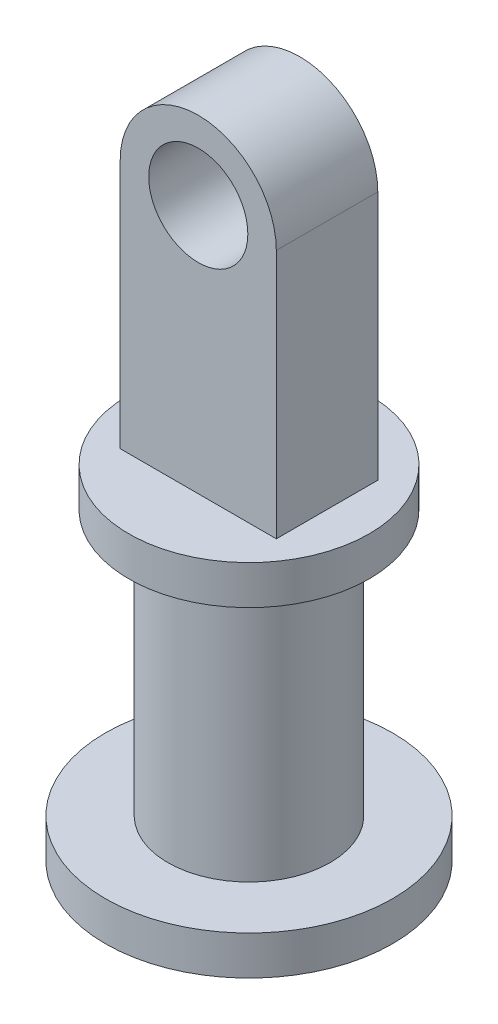
SolidWorks part; units mm, degrees
material "ABS"
ref_plane "Front Plane" through (0, 0, 0) normal (0, 0, 1) x (1, 0, 0)
ref_plane "Top Plane" through (0, 0, 0) normal (0, 1, 0) x (1, 0, 0)
ref_plane "Right Plane" through (0, 0, 0) normal (1, 0, 0) x (0, 0, -1)
sketch "Sketch1" plane through (0, 0, 0) normal (0, 0, 1) x (1, 0, 0)
  line L0 (2.5, 0) -> (2.5, -8)
  line L1 (2.5, -8) -> (-2.5, -8)
  line L2 (-2.5, -8) -> (-2.5, 0)
  arc A0 (2.5, 0) -> (-2.5, 0) centre (0, 0) ccw
  circle A1 centre (0, 0) radius 1.5875
extrude "Boss-Extrude1" add sketch "Sketch1" along normal blind 3.25
sketch "Sketch3" plane through (0, 0, 3.25) normal (0, 0, 1) x (1, 0, 0)
  line L0 (-2.5, -8) -> (-2.5, -18)
  line L1 (-2.5, -18) -> (-6.25, -18)
  line L2 (-6.25, -18) -> (-6.25, -19.5)
  line L3 (0, 0) -> (0, -8) construction
  line L4 (-2.5, -8) -> (2.5, -8) construction
  line L5 (-6.25, -19.5) -> (0.0103, -19.5)
  line L6 (2.5, -8) -> (2.5, -18)
  line L7 (6.25, -19.5) -> (-0.0103, -19.5)
  line L8 (6.25, -18) -> (6.25, -19.5)
  line L9 (2.5, -18) -> (6.25, -18)
ref_plane "Plane1" through (0, 0, 1.625) normal (0, 0, 1) x (1, 0, 0)
sketch "Sketch4" plane through (0, 0, 1.625) normal (0, 0, 1) x (1, 0, 0)
  line L0 (-2.6, -8) -> (2.6, -8)
  line L1 (-2.6, -9.25) -> (-2.6, -18)
  line L2 (-2.6, -18) -> (-4.6, -18)
  line L3 (-1.35, -19.25) -> (-4.6, -19.25)
  line L4 (4.6, -18.9948) -> (4.6, -17.7448)
  line L5 (2.6, -9.25) -> (2.6, -17.7448)
  line L6 (2.6, -17.7448) -> (4.6, -17.7448)
  line L7 (-4.6, -18) -> (-4.6, -19.25)
  line L8 (0, -19.5) -> (0, 2.5) construction
  line L9 (-1.35, -19.25) -> (-1.35, -9.25)
  line L10 (-1.35, -9.25) -> (1.35, -9.25)
  line L11 (1.35, -9.25) -> (1.35, -18.9948)
  line L12 (1.35, -18.9948) -> (4.6, -18.9948)
  line L13 (-2.5, -8) -> (2.5, -8) construction
  line L14 (2.6, -9.25) -> (3.85, -9.25)
  line L15 (3.85, -9.25) -> (3.85, -8)
  line L16 (3.85, -8) -> (2.6, -8)
  line L17 (-2.6, -8) -> (-3.85, -8)
  line L18 (-3.85, -8) -> (-3.85, -9.25)
  line L19 (-3.85, -9.25) -> (-2.6, -9.25)
  arc A0 (2.5, 0) -> (-2.5, 0) centre (0, 0) ccw construction
  point P15 (0, -8)
  dimension "D1" = 1.25
  dimension "D2" = 1.25
  dimension "D3" = 1.25
  dimension "D4" = 2.6
  dimension "D5" = 2
  dimension "D6" = 1.25
  dimension "D7" = 1.25
  dimension "D8" = 1.25
  dimension "D9" = 1.25
  dimension "D10" = 1.25
  dimension "D11" = 1.25
revolve "Revolve1" add sketch "Sketch4" angle 360 about L8
sketch "Sketch5" plane through (0, 0, 1.625) normal (0, 0, 1) x (1, 0, 0)
  line L0 (-6.35, -49.5) -> (-6.35, -16)
  line L1 (4.6, -17.7448) -> (-4.6, -17.7448) construction
  line L3 (-6.35, -16) -> (-3.1, -16)
  line L4 (-6.35, -49.5) -> (-7.85, -49.5)
  line L5 (-7.85, -49.5) -> (-7.85, -51)
  line L6 (0, 0) -> (0, -25.592) construction
  line L7 (-7.85, -51) -> (-5.1, -51)
  line L8 (-3.1, -16) -> (-3.1, -17.2448)
  line L9 (-3.1, -17.2448) -> (-5.1, -17.2448)
  line L10 (-5.1, -17.2448) -> (-5.1, -51)
  line L12 (-2.6, -9.25) -> (-2.6, -17.7448) construction
  dimension "D1" = 1.25
  dimension "D2" = 0.5
  dimension "D3" = 35
  dimension "D4" = 0.5
  dimension "D5" = 3.25
  dimension "D6" = 1.5
revolve "Revolve2" [suppressed] add sketch "Sketch5" angle 360 about L6
sketch "Sketch6" [suppressed] plane through (0, 0, 1.8) normal (0, 0, 1) x (1, 0, 0)
  line L0 (0, 0) -> (0, -44.2767) construction
  line L1 (-9.469, -48.5) -> (-9.469, -47)
  line L2 (-9.469, -47) -> (-12.719, -47)
  line L3 (-12.719, -47) -> (-12.719, -82)
  line L4 (-9.469, -48.5) -> (-11.219, -48.5)
  line L5 (-11.219, -48.5) -> (-11.219, -83.5)
  line L6 (-14.469, -82) -> (-14.469, -83.5)
  line L7 (-14.469, -83.5) -> (-11.219, -83.5)
  line L8 (-14.469, -82) -> (-12.719, -82)
  line L10 (10.25, -49.5) -> (-10.25, -49.5) construction
  dimension "D1" = 1.5
  dimension "D2" = 1
  dimension "D3" = 1.5
  dimension "D4" = 35
revolve "Revolve3" [suppressed] add sketch "Sketch6" angle 360 about L0
